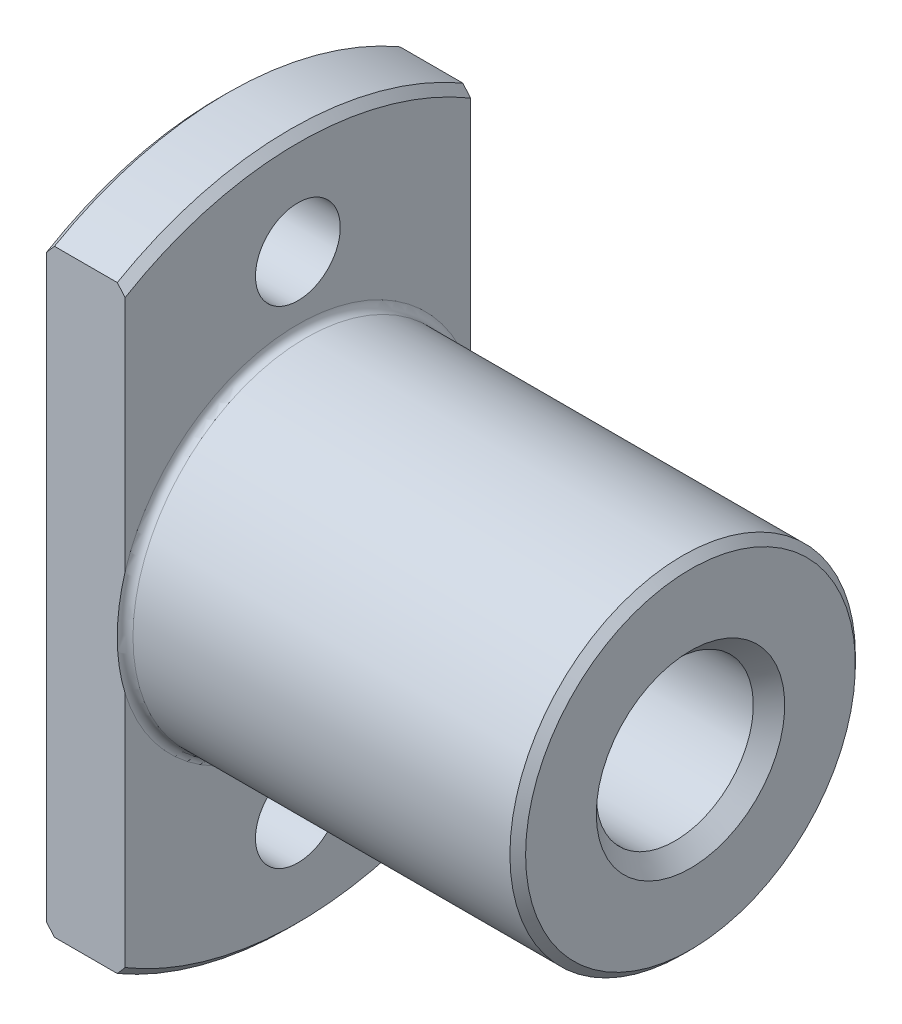
SolidWorks part; units mm, degrees
material "Delrin 2700 NC010, Low Viscosity Acetal Copolymer (SS)"
ref_plane "Front Plane" through (0, 0, 0) normal (0, 0, 1) x (1, 0, 0)
ref_plane "Top Plane" through (0, 0, 0) normal (0, 1, 0) x (1, 0, 0)
ref_plane "Right Plane" through (0, 0, 0) normal (1, 0, 0) x (0, 0, -1)
ref_plane "Plane1" through (0, 0, 0) normal (0, 0, 1) x (1, 0, 0)
sketch "Sketch1" plane through (0, 0, 0) normal (0, 0, 1) x (1, 0, 0)
  line L0 (0, 0) -> (0, 21.5)
  line L1 (0, 21.5) -> (0.5, 22)
  line L2 (0.5, 22) -> (4.5, 22)
  line L3 (4.5, 22) -> (5, 21.5)
  line L4 (5, 21.5) -> (5, 11.5)
  line L5 (5.5, 11) -> (29.5, 11)
  line L6 (29.5, 11) -> (30, 10.5)
  line L7 (30, 10.5) -> (30, 0)
  line L8 (30, 0) -> (0, 0)
  line L9 (30, 0) -> (0, 0) construction
  arc A0 (5, 11.5) -> (5.5, 11) centre (5.5, 11.5) ccw
revolve "Revolve1" add sketch "Sketch1" angle 360 about L9
ref_plane "Plane2" through (0, 0, 0) normal (0, 0, 1) x (1, 0, 0)
sketch "Sketch2" plane through (0, 0, 0) normal (0, 0, 1) x (1, 0, 0)
  line L0 (0, 0) -> (0, 6)
  line L1 (0, 6) -> (1, 5)
  line L2 (1, 5) -> (29, 5)
  line L3 (29, 5) -> (30, 6)
  line L4 (30, 6) -> (30, 0)
  line L5 (30, 0) -> (0, 0)
  line L6 (30, 0) -> (0, 0) construction
revolve "Cut-Revolve1" cut sketch "Sketch2" angle 360 about L6
cosmetic thread "Cosmetic Thread1" parameters "D1"=30, "D2"=12
ref_plane "Plane3" through (0, 0, 0) normal (0, 0, 1) x (1, 0, 0)
sketch "Sketch3" plane through (0, 0, 0) normal (0, 0, 1) x (1, 0, 0)
  line L0 (0, 15.5) -> (0, 18.2)
  line L1 (0, 18.2) -> (5, 18.2)
  line L2 (5, 18.2) -> (5, 15.5)
  line L3 (5, 15.5) -> (0, 15.5)
  line L4 (5, 15.5) -> (0, 15.5) construction
revolve "Cut-Revolve2" cut sketch "Sketch3" angle 360 about L4
ref_plane "Plane4" through (0, 0, 15.5) normal (0, 0, 1) x (1, 0, 0)
sketch "Sketch4" plane through (0, 0, 15.5) normal (0, 0, 1) x (1, 0, 0)
  line L0 (0, 0) -> (0, 2.7)
  line L1 (0, 2.7) -> (5, 2.7)
  line L2 (5, 2.7) -> (5, 0)
  line L3 (5, 0) -> (0, 0)
  line L4 (5, 0) -> (0, 0) construction
revolve "Cut-Revolve3" cut sketch "Sketch4" angle 360 about L4
ref_plane "Plane5" through (0, 0, 0) normal (0, 0, 1) x (1, 0, 0)
sketch "Sketch5" plane through (0, 0, 0) normal (0, 0, 1) x (1, 0, 0)
  line L0 (0, -15.5) -> (0, -12.8)
  line L1 (0, -12.8) -> (5, -12.8)
  line L2 (5, -12.8) -> (5, -15.5)
  line L3 (5, -15.5) -> (0, -15.5)
  line L4 (5, -15.5) -> (0, -15.5) construction
revolve "Cut-Revolve4" cut sketch "Sketch5" angle 360 about L4
ref_plane "Plane6" through (0, 0, -15.5) normal (0, 0, 1) x (1, 0, 0)
sketch "Sketch6" plane through (0, 0, -15.5) normal (0, 0, 1) x (1, 0, 0)
  line L0 (0, 0) -> (0, 2.7)
  line L1 (0, 2.7) -> (5, 2.7)
  line L2 (5, 2.7) -> (5, 0)
  line L3 (5, 0) -> (0, 0)
  line L4 (5, 0) -> (0, 0) construction
revolve "Cut-Revolve5" cut sketch "Sketch6" angle 360 about L4
sketch "Sketch7" plane through (0, 0, 0) normal (-1, 0, 0) x (0, 0, 1)
  line L0 (0, 25.3152) -> (0, -29.2317) construction
  line L1 (11, 19.0526) -> (11, -19.0526)
  line L2 (-11, 19.0526) -> (-11, -19.0526)
  arc A1 (-11, -19.0526) -> (-11, 19.0526) centre (0, 0) cw
  arc A2 (11, -19.0526) -> (11, 19.0526) centre (0, 0) ccw
  dimension "D2" = 22
  dimension "D1" = 11
extrude "Cut-Extrude1" cut sketch "Sketch7" against normal up to surface (5 mm away) up to face at (5, -15.5, 2.7)
